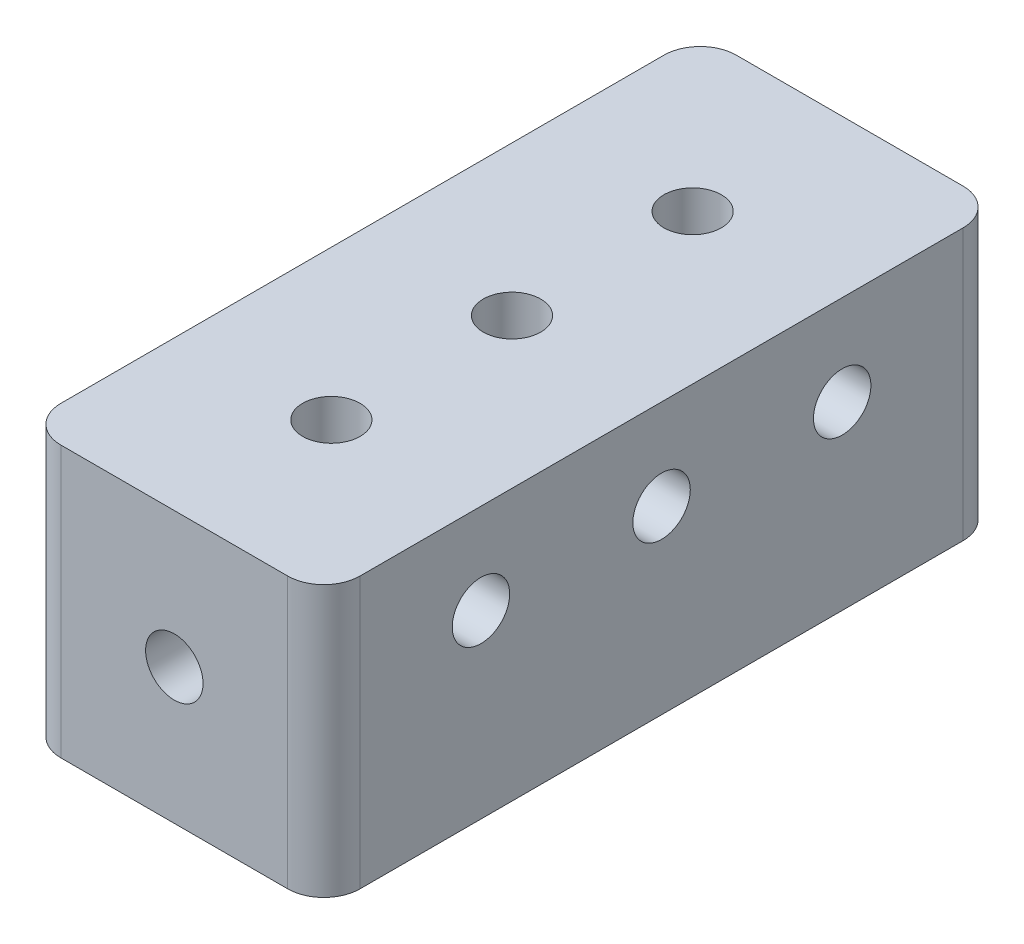
SolidWorks part; units mm, degrees
material "6061-T6 (SS)"
ref_plane "Front Plane" through (0, 0, 0) normal (0, 0, 1) x (1, 0, 0)
ref_plane "Top Plane" through (0, 0, 0) normal (0, 1, 0) x (1, 0, 0)
ref_plane "Right Plane" through (0, 0, 0) normal (1, 0, 0) x (0, 0, -1)
sketch "Sketch1" plane through (0, 0, 0) normal (0, 1, 0) x (1, 0, 0)
  line L1 (-10.5156, -23.7427) -> (10.5156, -23.7427)
  line L2 (-10.5156, -23.7427) -> (-10.5156, 23.7426)
  line L3 (-10.5156, 23.7426) -> (10.5156, 23.7426)
  line L4 (10.5156, -23.7427) -> (10.5156, 23.7426)
  line L5 (-10.5156, -23.7427) -> (10.5156, 23.7426) construction
  line L6 (-10.5156, 23.7426) -> (10.5156, -23.7427) construction
  point P0 (0, 0)
  dimension "D1" = 21.0312
  dimension "D2" = 47.4853
extrude "Boss-Extrude1" add sketch "Sketch1" along normal mid plane 19.05
sketch "Sketch2" plane through (0, 0, 23.7427) normal (0, 0, 1) x (1, 0, 0)
  circle A0 centre (0, 0) radius 2.0193
  dimension "D3" = 4.0386
extrude "Cut-Extrude1" cut sketch "Sketch2" against normal blind 9.525
sketch "Sketch3" plane through (0, 0, -23.7426) normal (0, 0, -1) x (-1, 0, 0)
  circle A0 centre (0, 0) radius 2.0193 construction
  circle A1 centre (0, 0) radius 2.0193
extrude "Cut-Extrude2" cut sketch "Sketch3" against normal blind 9.525
sketch "Sketch4" plane through (10.5156, 0, 0) normal (1, 0, 0) x (0, 0, -1)
  line L0 (-23.7427, 9.525) -> (23.7426, 9.525) construction
  circle A0 centre (-12.7, 3.175) radius 2.0193
  circle A1 centre (12.7, 3.175) radius 2.0193
  circle A2 centre (0, 3.175) radius 2.0193
  dimension "D5" = 4.0386
  dimension "D1" = 6.35
  dimension "D3" = 12.7
  dimension "D4" = 12.7
extrude "Cut-Extrude3" cut sketch "Sketch4" against normal blind 6.35
sketch "Sketch5" plane through (-10.5156, 0, 0) normal (-1, 0, 0) x (0, 0, 1)
  circle A0 centre (-12.7, 3.175) radius 2.0193 construction
  circle A1 centre (0, 3.175) radius 2.0193 construction
  circle A2 centre (12.7, 3.175) radius 2.0193 construction
  circle A3 centre (-12.7, 3.175) radius 2.0193
  circle A4 centre (0, 3.175) radius 2.0193
  circle A5 centre (12.7, 3.175) radius 2.0193
extrude "Cut-Extrude4" cut sketch "Sketch5" against normal blind 6.35
sketch "Sketch6" plane through (0, 9.525, 0) normal (0, 1, 0) x (1, 0, 0)
  line L1 (-10.5156, 23.7426) -> (-10.5156, -23.7427) construction
  circle A0 centre (0, 12.7) radius 2.0193
  circle A1 centre (0, 0) radius 2.0193
  circle A2 centre (0, -12.7) radius 2.0193
  dimension "D1" = 4.0386
  dimension "D6" = 10.5156
  dimension "D2" = 12.7
  dimension "D3" = 12.7
extrude "Cut-Extrude5" cut sketch "Sketch6" against normal blind 6.35
fillet "Fillet1" radius 2.54 4 edges at (10.5156, 0, 23.7427) (-10.5156, 0, 23.7427) (-10.5156, 0, -23.7426) (10.5156, 0, -23.7426)
